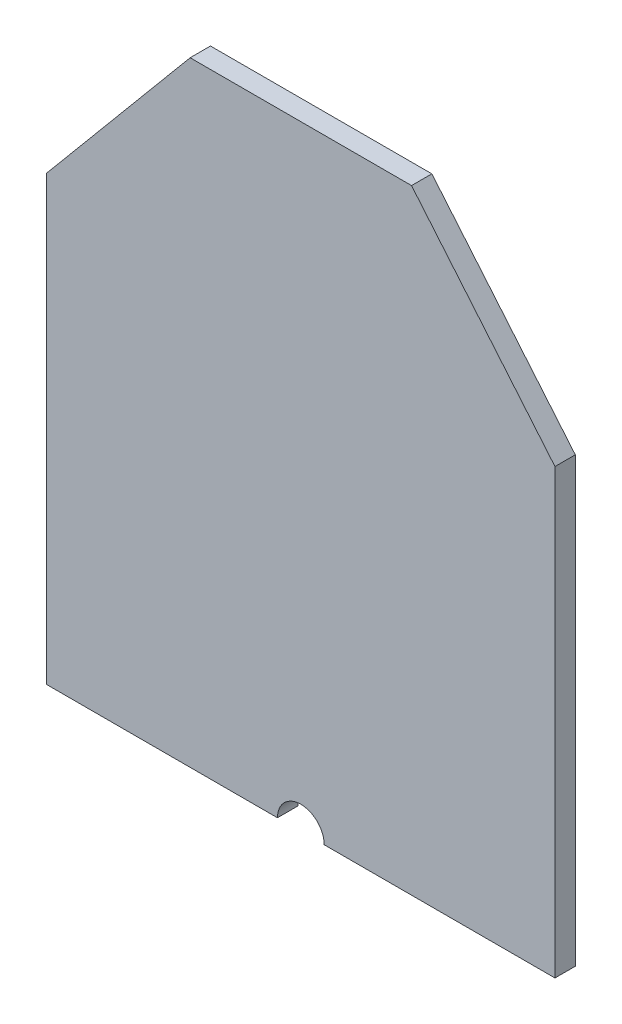
SolidWorks part; units mm, degrees
ref_plane "Front Plane" through (0, 0, 0) normal (0, 0, 1) x (1, 0, 0)
ref_plane "Top Plane" through (0, 0, 0) normal (0, 1, 0) x (1, 0, 0)
ref_plane "Right Plane" through (0, 0, 0) normal (1, 0, 0) x (0, 0, -1)
sketch "Sketch1" plane through (0, 0, 0) normal (0, 0, 1) x (1, 0, 0)
  line L0 (-11.5, -108.94) -> (-125, -108.94)
  line L2 (125, 108.94) -> (125, -108.94)
  line L3 (125, -108.94) -> (11.5, -108.94)
  line L4 (-125, 108.94) -> (-125, -108.94)
  line L5 (125, 108.94) -> (54.45, 193.35)
  line L6 (-54.45, 193.35) -> (54.45, 193.35)
  line L7 (-125, 108.94) -> (-54.45, 193.35)
  arc A0 (11.5, -108.94) -> (-11.5, -108.94) centre (0, -108.94) ccw
  point P0 (0, 0)
  dimension "D3" = 23
  dimension "D1" = 217.88
  dimension "D2" = 250
  dimension "D4" = 70.55
  dimension "D5" = 84.41
  dimension "D6" = 70.55
extrude "Boss-Extrude2" add sketch "Sketch1" along normal mid plane 10
